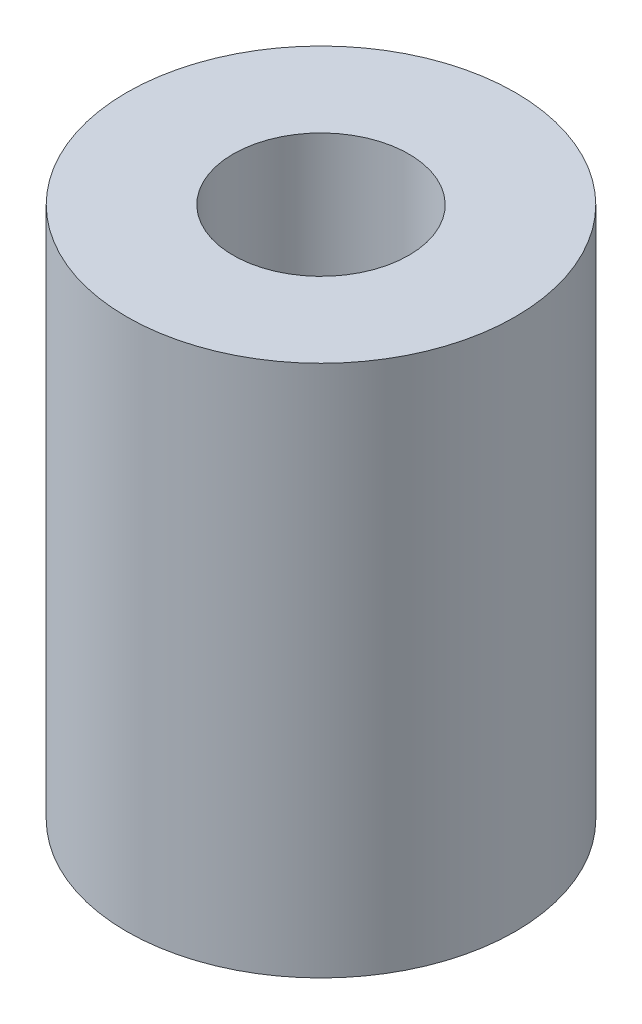
SolidWorks part; units mm, degrees
ref_plane "Front Plane" through (0, 0, 0) normal (0, 0, 1) x (1, 0, 0)
ref_plane "Top Plane" through (0, 0, 0) normal (0, 1, 0) x (1, 0, 0)
ref_plane "Right Plane" through (0, 0, 0) normal (1, 0, 0) x (0, 0, -1)
sketch "Sketch1" plane through (0, 0, 0) normal (0, 0, 1) x (1, 0, 0)
  line L0 (0, 10) -> (0, -15) construction
  line L1 (4.125, 10) -> (9.125, 10)
  line L2 (9.125, 10) -> (9.125, -15)
  line L3 (9.125, -15) -> (1.5, -15)
  line L4 (1.5, -15) -> (1.5, 0)
  line L5 (1.5, 0) -> (4.125, 0)
  line L6 (4.125, 0) -> (4.125, 10)
  point P4 (7.7604, 0)
  point P10 (0, 0)
  dimension "D1" = 5
  dimension "D2" = 8.25
  dimension "D3" = 3
  dimension "D4" = 25
  dimension "D5" = 10
revolve "Revolve1" add sketch "Sketch1" angle 360 about L0
